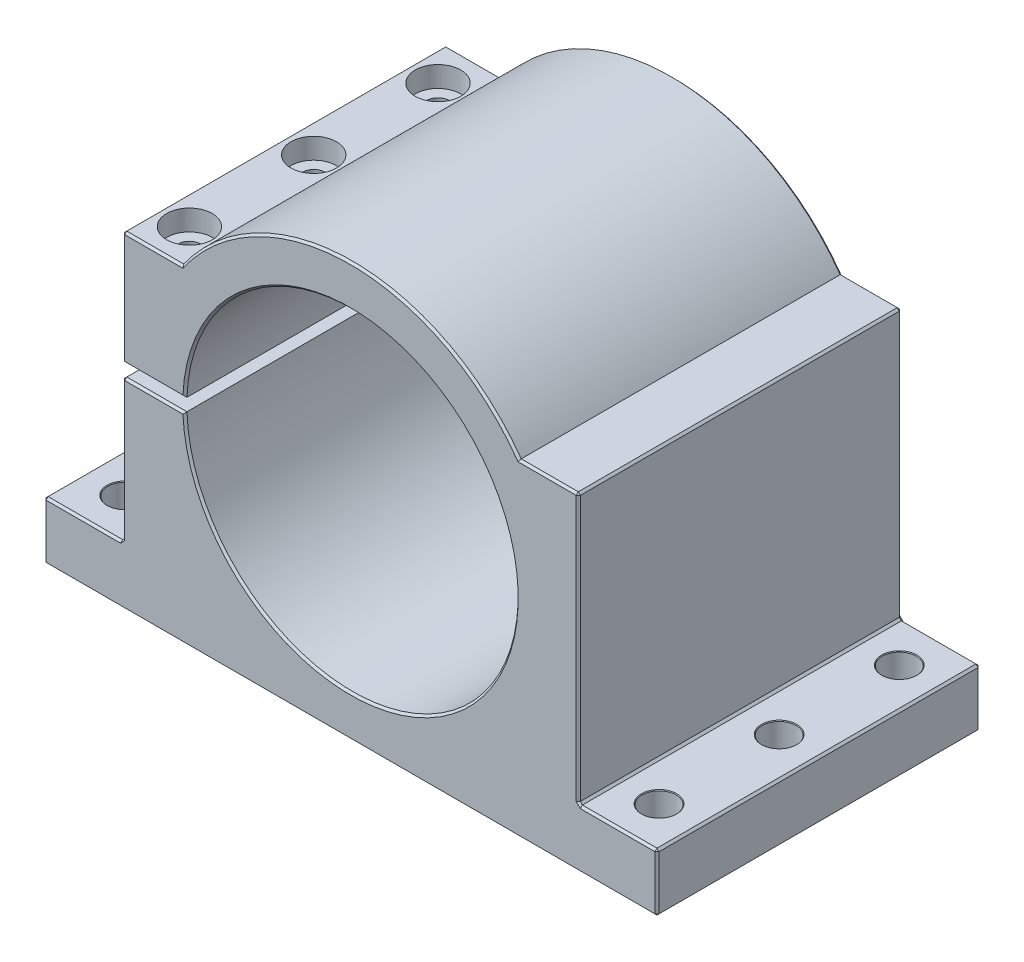
SolidWorks part; units mm, degrees
material "1060 Сплав"
ref_plane "Спереди" through (0, 0, 0) normal (0, 0, 1) x (1, 0, 0)
ref_plane "Сверху" through (0, 0, 0) normal (0, 1, 0) x (1, 0, 0)
ref_plane "Справа" through (0, 0, 0) normal (1, 0, 0) x (0, 0, -1)
sketch "Эскиз1" plane through (0, 0, 0) normal (0, 0, 1) x (1, 0, 0)
  line L0 (0, 0) -> (0, -50) construction
  line L1 (74, -50) -> (-74, -50)
  line L2 (-74, -50) -> (-74, -36)
  line L3 (-74, -36) -> (-55, -36)
  line L4 (-55, -36) -> (-55, 29)
  line L5 (-55, 29) -> (-40.7308, 29)
  line L6 (0, 29) -> (-40.7308, 29) construction
  line L7 (-55, 1.5) -> (0, 1.5)
  line L8 (-55, 1.5) -> (-55, -1.5)
  line L9 (-55, -1.5) -> (0, -1.5)
  line L10 (0, 1.5) -> (0, -1.5)
  line L11 (0, 29) -> (0, 0) construction
  line L12 (0, -50) -> (0, 50) construction
  line L13 (55, 29) -> (40.7308, 29)
  line L14 (55, -36) -> (55, 29)
  line L15 (74, -36) -> (55, -36)
  line L16 (74, -50) -> (74, -36)
  circle A0 centre (0, 0) radius 40
  circle A2 centre (0, 0) radius 50
  point P13 (-27.55, 29)
  point P20 (0, 40)
  dimension "D1" = 80
  dimension "D2" = 3
  dimension "D3" = 50
  dimension "D4" = 14
  dimension "D5" = 148
  dimension "D6" = 19
  dimension "D7" = 65
  dimension "D8" = 10
extrude "Бобышка-Вытянуть1" add sketch "Эскиз1" along normal mid plane 78 contours A2 L1 L16 L15 L14 L13 | A2 L7 A0 L9 | A2 L9 L4 L3 L2 L1 | A2 L5 L4 L7
sketch "Эскиз2" plane through (0, 29, 0) normal (0, 1, 0) x (1, 0, 0)
  line L0 (-47.8654, 39) -> (-47.8654, -39) construction
  line L1 (-55, 39) -> (-40.7308, 39) construction
  line L2 (-55, -39) -> (-40.7308, -39) construction
  circle A0 centre (-47.8654, 30) radius 5.5
  circle A1 centre (-47.8654, 0) radius 5.5
  circle A2 centre (-47.8654, -30) radius 5.5
  dimension "D1" = 11
  dimension "D2" = 11
  dimension "D3" = 11
  dimension "D4" = 30
  dimension "D5" = 30
extrude "Вырез-Вытянуть1" cut sketch "Эскиз2" against normal blind 5
sketch "Эскиз3" plane through (0, 24, 0) normal (0, 1, 0) x (1, 0, 0)
  circle A0 centre (-47.8654, 30) radius 2.75
  circle A1 centre (-47.8654, 0) radius 2.75
  circle A2 centre (-47.8654, -30) radius 2.75
  dimension "D1" = 5.5
extrude "Вырез-Вытянуть2" cut sketch "Эскиз3" against normal up to surface (25.5 mm away) up to face at (-47.4859, -1.5, 0)
sketch "Эскиз4" plane through (0, -1.5, 0) normal (0, 1, 0) x (1, 0, 0)
  circle A0 centre (-47.8654, 30) radius 2.1
  circle A1 centre (-47.8654, 0) radius 2.1
  circle A2 centre (-47.8654, -30) radius 2.1
  dimension "D1" = 4.2
extrude "Вырез-Вытянуть3" cut sketch "Эскиз4" against normal blind 30
hole_wizard "HoleWzd1" positions "Sketch2" profile "Sketch3" legacy
sketch "Sketch2" plane through (0, -36, 0) normal (0, 1, 0) x (1, 0, 0)
  line L4 (0, 0) -> (0, 54.1081) construction
  line L7 (-74, 39) -> (-55, 39) construction
  line L8 (-74, -39) -> (-74, 39) construction
  line L9 (-74, -39) -> (-55, -39) construction
  point P0 (-64.5, 29)
  point P2 (-64.5, 0)
  point P4 (-64.5, -29)
  point P22 (64.5, -29)
  point P23 (64.5, 0)
  point P24 (64.5, 29)
  dimension "D1" = 10
  dimension "D2" = 9.5
  dimension "D3" = 10
sketch "Sketch3" plane through (-64.5, -36, -29) normal (1, 0, 0) x (0, 0, 1)
  line L0 (0, 0) -> (0, 16)
  line L1 (0, 16) -> (4.1, 16)
  line L2 (4.1, 16) -> (4.1, 0.1726)
  line L3 (4.1, 0.1726) -> (4.25, 0)
  line L4 (4.25, 0) -> (0, 0)
  line L5 (0, -6.4453) -> (0, 115.525) construction
  line L6 (-4.1, 0.1726) -> (-4.25, 0) construction
  dimension "Диаметр" = 8.2
  dimension "Глубина" = 16
  dimension "Угол зенк." = 82
  dimension "Диа. зенковки" = 8.5
chamfer "Chamfer1" distance 0.5 angle 45 38 edges at (74, -50, 0) (74, -36, 0) (-74, -36, 0) (55, -3.5, -39) (55, -3.5, 39) (64.5, -36, -39) (64.5, -36, 39) (74, -43, -39) (74, -43, 39) (0, -50, -39) (0, -50, 39) (47.8654, 29, -39) (47.8654, 29, 39) (0, 50, -39) (0, 50, 39) (-47.8654, 29, -39) (-47.8654, 29, 39) (-55, 15.25, -39) (-55, 15.25, 39) (-47.4859, 1.5, -39) (-47.4859, 1.5, 39) (40, 0, -39) (40, 0, 39) (-47.4859, -1.5, -39) (-47.4859, -1.5, 39) (-55, -18.75, -39) (-55, -18.75, 39) (-64.5, -36, -39) (-64.5, -36, 39) (-74, -43, -39) (-74, -43, 39) (-74, -50, 0) (-55, -1.5, 0) (-55, -36, 0) (-55, 29, 0) (-55, 1.5, 0) (55, -36, 0) (55, 29, 0)
